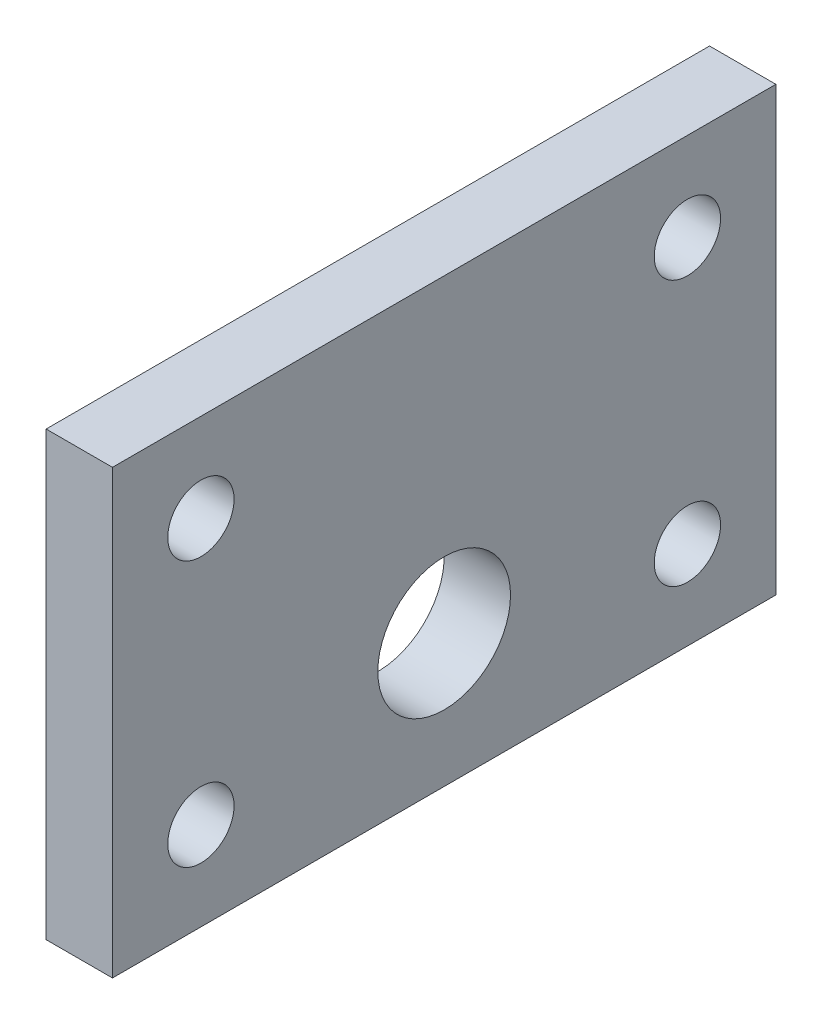
SolidWorks part; units mm, degrees
ref_plane "Front" through (0, 0, 0) normal (0, 0, 1) x (1, 0, 0)
ref_plane "Top" through (0, 0, 0) normal (0, 1, 0) x (1, 0, 0)
ref_plane "Right" through (0, 0, 0) normal (1, 0, 0) x (0, 0, -1)
sketch "草图1" plane through (0, 0, 0) normal (1, 0, 0) x (0, 0, -1)
  line L0 (-15, 0) -> (15, 0) construction
  line L1 (15, -10) -> (-15, -10)
  line L2 (15, -10) -> (15, 10)
  line L3 (15, 10) -> (-15, 10)
  line L4 (-15, -10) -> (-15, 10)
  line L5 (15, -10) -> (-15, 10) construction
  line L6 (15, 10) -> (-15, -10) construction
  circle A0 centre (0, 0) radius 3 construction
  circle A1 centre (-11, 6) radius 1.5
  circle A2 centre (-11, -6) radius 1.5
  circle A3 centre (11, -6) radius 1.5
  circle A4 centre (11, 6) radius 1.5
  point P0 (0, 0)
  dimension "D1" = 6
  dimension "D4" = 3
  dimension "D5" = 3
  dimension "D8" = 22
  dimension "D2" = 30
  dimension "D3" = 20
  dimension "D6" = 4
  dimension "D7" = 6
  dimension "D9" = 22
extrude "凸台-拉伸1" add sketch "草图1" along normal blind 3
sketch "草图2" plane through (0, 0, 0) normal (-1, 0, 0) x (0, 0, 1)
  line L0 (0, -10) -> (0, 10) construction
  line L1 (15, -10) -> (-15, -10) construction
  line L2 (-15, 10) -> (15, 10) construction
  circle A0 centre (0, -4) radius 3
  dimension "D1" = 6
  dimension "D2" = 14
extrude "切除-拉伸1" cut sketch "草图2" against normal up to next
